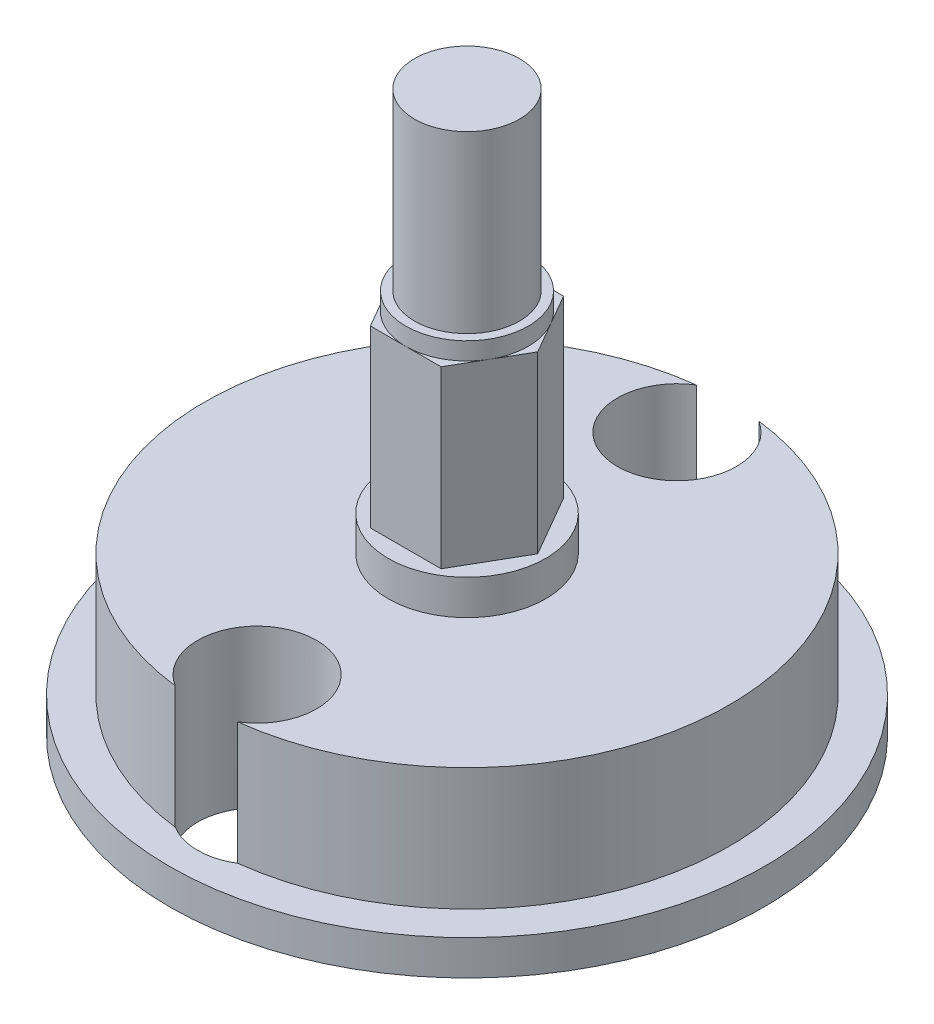
SolidWorks part; units mm, degrees
ref_plane "正面" through (0, 0, 0) normal (0, 0, 1) x (1, 0, 0)
ref_plane "平面" through (0, 0, 0) normal (0, 1, 0) x (1, 0, 0)
ref_plane "右側面" through (0, 0, 0) normal (1, 0, 0) x (0, 0, -1)
sketch "ｽｹｯﾁ1" plane through (0, 0, 0) normal (0, 1, 0) x (1, 0, 0)
  circle A0 centre (0, 0) radius 7.5
  dimension "D1" = 15
extrude "ﾎﾞｽ - 押し出し1" add sketch "ｽｹｯﾁ1" along normal blind 4.5
sketch "ｽｹｯﾁ9" plane through (0, 4.5, 0) normal (0, 1, 0) x (1, 0, 0)
  circle A0 centre (0, 0) radius 2.25
  dimension "D1" = 4.5
extrude "ﾎﾞｽ - 押し出し6" add sketch "ｽｹｯﾁ9" along normal blind 1
sketch "ｽｹｯﾁ2" plane through (0, 5.5, 0) normal (0, 1, 0) x (1, 0, 0)
  line L1 (2.0207, 0) -> (1.0104, 1.75)
  line L2 (1.0104, 1.75) -> (-1.0104, 1.75)
  line L3 (-1.0104, 1.75) -> (-2.0207, 0)
  line L4 (-2.0207, 0) -> (-1.0104, -1.75)
  line L5 (-1.0104, -1.75) -> (1.0104, -1.75)
  line L6 (1.0104, -1.75) -> (2.0207, 0)
  circle A0 centre (0, 0) radius 1.75 construction
  dimension "D1" = 3.5
extrude "ﾎﾞｽ - 押し出し2" add sketch "ｽｹｯﾁ2" along normal blind 5
sketch "ｽｹｯﾁ6" plane through (0, 10.5, 0) normal (0, 1, 0) x (1, 0, 0)
  line L0 (2.0207, 0) -> (1.0104, 1.75) construction
  circle A0 centre (0, 0) radius 1.75
extrude "ﾎﾞｽ - 押し出し3" add sketch "ｽｹｯﾁ6" along normal blind 0.5
sketch "ｽｹｯﾁ7" plane through (0, 11, 0) normal (0, 1, 0) x (1, 0, 0)
  circle A0 centre (0, 0) radius 1.5
  dimension "D1" = 3
extrude "ﾎﾞｽ - 押し出し4" add sketch "ｽｹｯﾁ7" along normal blind 5
sketch "ｽｹｯﾁ8" plane through (0, 0, 0) normal (0, -1, 0) x (-1, 0, 0)
  circle A0 centre (0, 0) radius 8.5
  circle A1 centre (0, 0) radius 7.5 construction
  circle A2 centre (0, 0) radius 7.5
  dimension "D1" = 1
extrude "ﾎﾞｽ - 押し出し5" add sketch "ｽｹｯﾁ8" against normal offset from surface (1 mm away) 3.5 up to face at (0, 4.5, 2.25)
hole_wizard "M3 すきま穴1" positions "ｽｹｯﾁ4" profile "ｽｹｯﾁ5" hole size "M3" standard "JIS" end condition through all
sketch "ｽｹｯﾁ4" plane through (0, 4.5, 0) normal (0, 1, 0) x (1, 0, 0)
  line L0 (0, 6) -> (0, -6) construction
  point P0 (0, 6)
  point P2 (0, -6)
  dimension "D1" = 12
sketch "ｽｹｯﾁ5" plane through (0, 4.5, -6) normal (1, 0, 0) x (0, 0, 1)
  line L0 (0, 0) -> (0, 4.5)
  line L1 (0, 4.5) -> (1.7, 4.5)
  line L2 (1.7, 4.5) -> (1.7, 0)
  line L5 (1.7, 0) -> (0, 0)
  line L11 (0, -6.35) -> (0, 107.95) construction
  dimension "通し穴の直径" = 3.4
  dimension "通し穴の深さ" = 4.5
